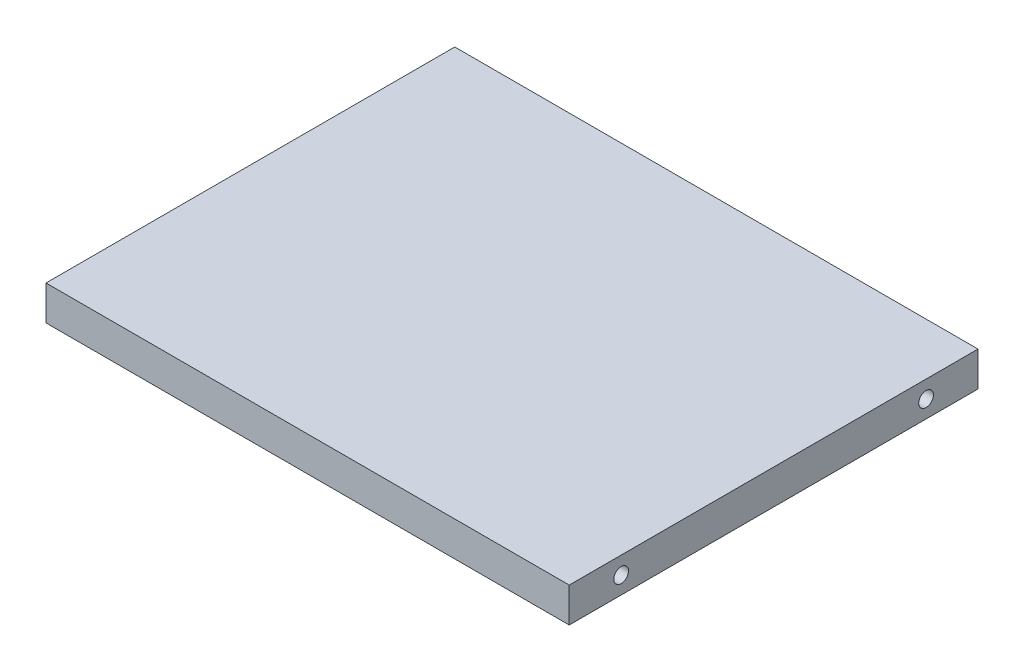
SolidWorks part; units mm, degrees
ref_plane "Front Plane" through (0, 0, 0) normal (0, 0, 1) x (1, 0, 0)
ref_plane "Top Plane" through (0, 0, 0) normal (0, 1, 0) x (1, 0, 0)
ref_plane "Right Plane" through (0, 0, 0) normal (1, 0, 0) x (0, 0, -1)
ref_plane "Plane1" through (0, 80, 0) normal (0, 1, 0) x (1, 0, 0)
sketch "Sketch1" plane through (0, 80, 0) normal (0, 1, 0) x (1, 0, 0)
  line L1 (96, 75) -> (0, 75)
  line L2 (96, 75) -> (96, 0)
  line L3 (96, 0) -> (0, 0)
  line L4 (0, 75) -> (0, 0)
extrude "Boss-Extrude1" add sketch "Sketch1" against normal blind 6.35
sketch "Sketch2" plane through (96, 0, 0) normal (1, 0, 0) x (0, 0, -1)
  circle A0 centre (65.475, 76.825) radius 1.3526
  circle A1 centre (9.525, 76.825) radius 1.3525
  circle A2 centre (65.475, 76.825) radius 1.8987 construction
  circle A3 centre (9.525, 76.825) radius 1.8987 construction
extrude "Cut-Extrude1" cut sketch "Sketch2" against normal blind 9.525
sketch "Sketch3" plane through (0, 0, 0) normal (-1, 0, 0) x (0, 0, 1)
  circle A0 centre (-65.475, 76.825) radius 1.3526
  circle A1 centre (-9.525, 76.825) radius 1.3525
  circle A2 centre (-65.475, 76.825) radius 1.8987 construction
  circle A3 centre (-9.525, 76.825) radius 1.8987 construction
extrude "Cut-Extrude2" cut sketch "Sketch3" against normal blind 9.525
